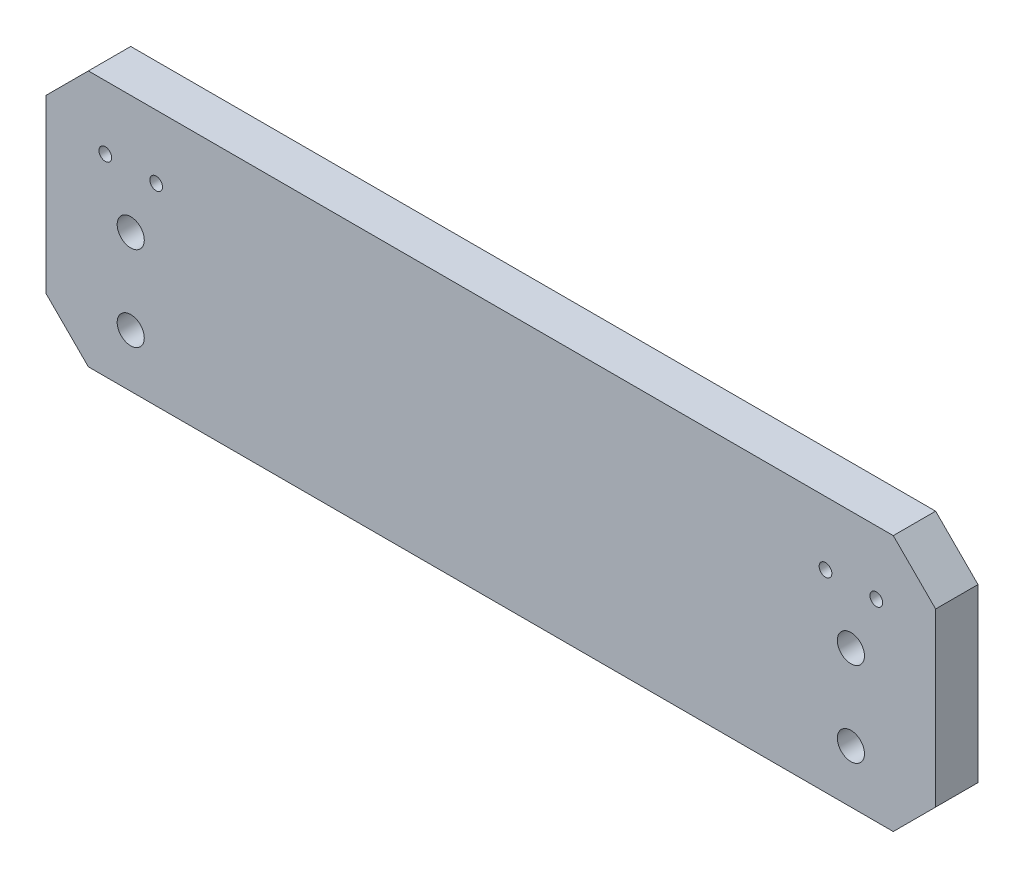
SolidWorks part; units mm, degrees
material "Pine"
ref_plane "Front Plane" through (0, 0, 0) normal (0, 0, 1) x (1, 0, 0)
ref_plane "Top Plane" through (0, 0, 0) normal (0, 1, 0) x (1, 0, 0)
ref_plane "Right Plane" through (0, 0, 0) normal (1, 0, 0) x (0, 0, -1)
sketch "Sketch1" plane through (0, 0, 0) normal (0, 0, 1) x (1, 0, 0)
  line L0 (-95, -7.75) -> (-75, -7.75) construction
  line L1 (-105, -30.25) -> (105, -30.25)
  line L2 (-105, -30.25) -> (-105, 30.25)
  line L3 (-105, 30.25) -> (105, 30.25)
  line L4 (105, -30.25) -> (105, 30.25)
  line L5 (-105, -30.25) -> (105, 30.25) construction
  line L6 (-105, 30.25) -> (105, -30.25) construction
  line L7 (-95, 12.25) -> (-75, 12.25) construction
  line L8 (-95, 12.25) -> (-95, -27.75) construction
  line L9 (-95, -27.75) -> (-75, -27.75) construction
  line L10 (-75, 12.25) -> (-75, -27.75) construction
  line L11 (-85, 12.25) -> (-85, -27.75) construction
  line L12 (0, 30.25) -> (0, -30.25) construction
  line L13 (95, -27.75) -> (75, -27.75) construction
  line L14 (75, 12.25) -> (75, -27.75) construction
  line L15 (95, -7.75) -> (75, -7.75) construction
  line L16 (95, 12.25) -> (95, -27.75) construction
  line L17 (85, 12.25) -> (85, -27.75) construction
  line L18 (95, 12.25) -> (75, 12.25) construction
  line L19 (-85, 20.25) -> (-85, 12.25) construction
  line L20 (-100, 20.25) -> (-70, 20.25) construction
  line L21 (-100, 20.25) -> (-100, 12.25) construction
  line L22 (-100, 12.25) -> (-70, 12.25) construction
  line L23 (-70, 20.25) -> (-70, 12.25) construction
  line L24 (70, 20.25) -> (70, 12.25) construction
  line L25 (100, 12.25) -> (70, 12.25) construction
  line L26 (100, 20.25) -> (100, 12.25) construction
  line L27 (100, 20.25) -> (70, 20.25) construction
  line L28 (85, 20.25) -> (85, 12.25) construction
  circle A0 centre (-85, 2.25) radius 3.2
  circle A1 centre (-85, -17.75) radius 3.2
  circle A2 centre (85, -17.75) radius 3.2
  circle A3 centre (85, 2.25) radius 3.2
  circle A4 centre (-91, 15.25) radius 1.5
  circle A5 centre (-79, 15.25) radius 1.5
  circle A6 centre (79, 15.25) radius 1.5
  circle A7 centre (91, 15.25) radius 1.5
  point P0 (0, 0)
  dimension "D3" = 40
  dimension "D6" = 6.4
  dimension "D9" = 3
  dimension "D11" = 30
  dimension "D12" = 3
  dimension "D2" = 10
  dimension "D4" = 20
  dimension "D5" = 20
  dimension "D7" = 2.5
  dimension "D8" = 170
  dimension "D10" = 8
  dimension "D13" = 12
  dimension "D14" = 10
extrude "Boss-Extrude1" add sketch "Sketch1" along normal blind 10
chamfer "Chamfer1" distance 10 angle 45 2 edges at (105, 30.25, 5) (-105, 30.25, 5)
chamfer "Chamfer2" distance 10 angle 45 2 edges at (105, -30.25, 5) (-105, -30.25, 5)
